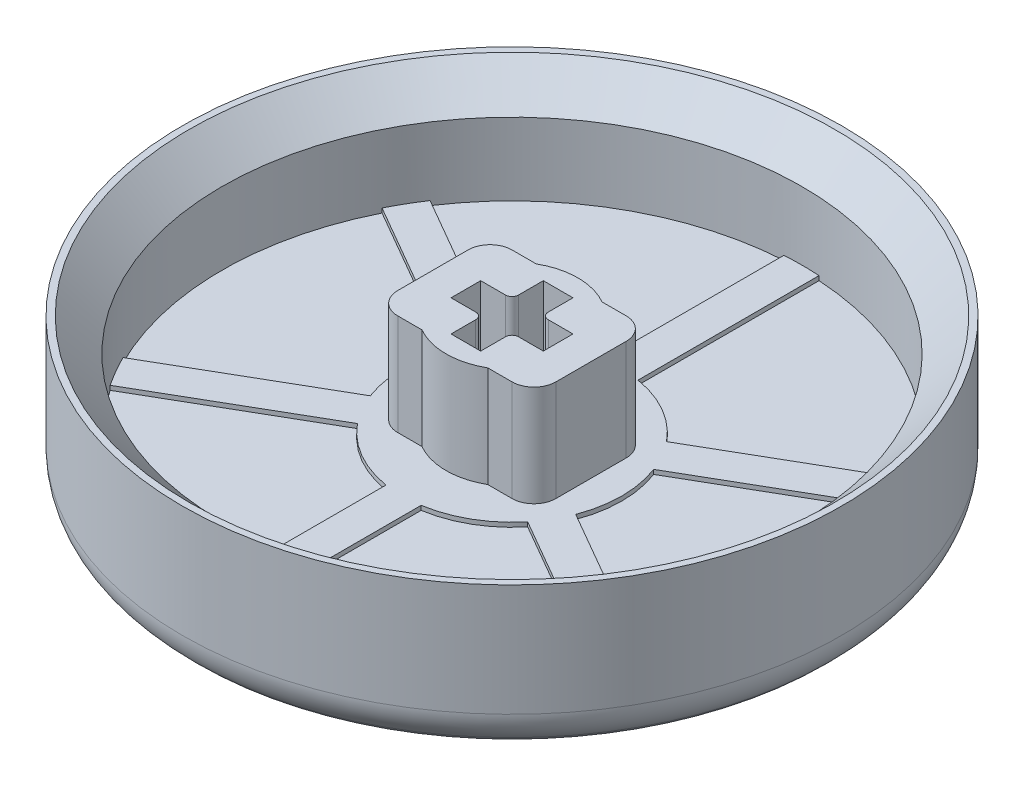
SolidWorks part; units mm, degrees
ref_plane "Front Plane" through (0, 0, 0) normal (0, 0, 1) x (1, 0, 0)
ref_plane "Top Plane" through (0, 0, 0) normal (0, 1, 0) x (1, 0, 0)
ref_plane "Right Plane" through (0, 0, 0) normal (1, 0, 0) x (0, 0, -1)
sketch "Sketch1" plane through (0, 0, 0) normal (0, 1, 0) x (1, 0, 0)
  circle A0 centre (0, 0) radius 15
  dimension "D1" = 30
extrude "button top" add sketch "Sketch1" along normal blind 1.8
sketch "Sketch2" plane through (0, 1.8, 0) normal (0, 1, 0) x (1, 0, 0)
  circle A3 centre (0, 0) radius 15
  circle A4 centre (0, 0) radius 15 construction
  circle A5 centre (0, 0) radius 13.2
  dimension "D1" = 1.8
extrude "button walls" add sketch "Sketch2" along normal blind 4.8
sketch "Sketch5" plane through (0, 1.8, 0) normal (0, 1, 0) x (1, 0, 0)
  circle A0 centre (0, 0) radius 5
  dimension "D1" = 10
extrude "offset" add sketch "Sketch5" along normal blind 0.2
sketch "Sketch3" plane through (0, 1.8, 0) normal (0, 1, 0) x (1, 0, 0)
  line L0 (0, -2.1) -> (0, 2.1) construction
  line L1 (-2.1, 0) -> (2.1, 0) construction
  line L2 (-0.675, 0.975) -> (-0.675, 2.1)
  line L3 (-0.675, -2.1) -> (0.675, -2.1)
  line L4 (-0.675, -2.1) -> (-0.675, -0.975)
  line L5 (-0.675, 2.1) -> (0.675, 2.1)
  line L6 (0.675, -2.1) -> (0.675, -0.975)
  line L7 (-0.675, -2.1) -> (0.675, 2.1) construction
  line L8 (-0.675, 2.1) -> (0.675, -2.1) construction
  line L9 (-2.1, -0.675) -> (-0.975, -0.675)
  line L10 (-2.1, -0.675) -> (-2.1, 0.675)
  line L11 (-2.1, 0.675) -> (-0.975, 0.675)
  line L12 (2.1, -0.675) -> (2.1, 0.675)
  line L13 (-2.1, -0.675) -> (2.1, 0.675) construction
  line L14 (-2.1, 0.675) -> (2.1, -0.675) construction
  line L15 (0.975, 0.675) -> (2.1, 0.675)
  line L16 (0.675, 0.975) -> (0.675, 2.1)
  line L17 (0.975, -0.675) -> (2.1, -0.675)
  line L19 (-3.6, -2.6) -> (3.6, -2.6)
  line L20 (-3.6, -2.6) -> (-3.6, 2.6)
  line L21 (-3.6, 2.6) -> (3.6, 2.6)
  line L22 (3.6, -2.6) -> (3.6, 2.6)
  line L23 (-3.6, -2.6) -> (3.6, 2.6) construction
  line L24 (-3.6, 2.6) -> (3.6, -2.6) construction
  arc A1 (-0.675, -0.975) -> (-0.975, -0.675) centre (-0.975, -0.975) ccw
  arc A2 (0.675, -0.975) -> (0.975, -0.675) centre (0.975, -0.975) cw
  arc A3 (0.975, 0.675) -> (0.675, 0.975) centre (0.975, 0.975) cw
  arc A4 (-0.675, 0.975) -> (-0.975, 0.675) centre (-0.975, 0.975) cw
  circle A5 centre (0, 0) radius 3
  point P0 (0, 0)
  point P6 (0, 0)
  point P9 (0, 0)
  point P22 (2.1, 0)
  point P24 (0, 2.1)
  point P29 (0.675, -0.675)
  point P32 (0.675, 0.675)
  dimension "D1" = 7.2
  dimension "D4" = 0.3
  dimension "D6" = 6
  dimension "D2" = 4.2
  dimension "D3" = 1.35
  dimension "D5" = 5.2
extrude "stem housing" add sketch "Sketch3" along normal blind 4.6 from surface at 0.2 contours A5 L21 L20 L19 | L19 A5 L21 A4 L2 L5 L16 A3 L15 L12 L17 A2 L6 L3 L4 A1 L9 L10 L11 | A5 L19 L22 L21 | L21 A5 | L19 A5 starting at face at (0, 2, 5)
sketch "Sketch4" plane through (0, 1.8, 0) normal (0, 1, 0) x (1, 0, 0)
  line L0 (0, 3.3382) -> (0, 13.2) construction
  line L1 (-0.8, 3.3382) -> (-0.8, 13.2)
  line L2 (0.8, 3.3382) -> (0.8, 13.2)
  line L3 (2.8909, 1.6691) -> (11.4315, 6.6) construction
  line L4 (2.4909, 2.3619) -> (11.0315, 7.2928)
  line L5 (3.2909, 0.9763) -> (11.8315, 5.9072)
  line L6 (2.8909, -1.6691) -> (11.4315, -6.6) construction
  line L7 (3.2909, -0.9763) -> (11.8315, -5.9072)
  line L8 (2.4909, -2.3619) -> (11.0315, -7.2928)
  line L9 (0, -3.3382) -> (0, -13.2) construction
  line L10 (0.8, -3.3382) -> (0.8, -13.2)
  line L11 (-0.8, -3.3382) -> (-0.8, -13.2)
  line L12 (-2.8909, -1.6691) -> (-11.4315, -6.6) construction
  line L13 (-2.4909, -2.3619) -> (-11.0315, -7.2928)
  line L14 (-3.2909, -0.9763) -> (-11.8315, -5.9072)
  line L15 (-2.8909, 1.6691) -> (-11.4315, 6.6) construction
  line L16 (-3.2909, 0.9763) -> (-11.8315, 5.9072)
  line L17 (-2.4909, 2.3619) -> (-11.0315, 7.2928)
  circle A2 centre (0, 0) radius 13.2 construction
  arc A3 (-0.8, 3.3382) -> (0.8, 3.3382) centre (0, 3.3382) ccw
  arc A4 (0.8, 13.2) -> (-0.8, 13.2) centre (0, 13.2) ccw
  arc A5 (2.4909, 2.3619) -> (3.2909, 0.9763) centre (2.8909, 1.6691) ccw
  arc A6 (11.8315, 5.9072) -> (11.0315, 7.2928) centre (11.4315, 6.6) ccw
  arc A7 (3.2909, -0.9763) -> (2.4909, -2.3619) centre (2.8909, -1.6691) ccw
  arc A8 (11.0315, -7.2928) -> (11.8315, -5.9072) centre (11.4315, -6.6) ccw
  arc A9 (0.8, -3.3382) -> (-0.8, -3.3382) centre (0, -3.3382) ccw
  arc A10 (-0.8, -13.2) -> (0.8, -13.2) centre (0, -13.2) ccw
  arc A11 (-2.4909, -2.3619) -> (-3.2909, -0.9763) centre (-2.8909, -1.6691) ccw
  arc A12 (-11.8315, -5.9072) -> (-11.0315, -7.2928) centre (-11.4315, -6.6) ccw
  arc A13 (-3.2909, 0.9763) -> (-2.4909, 2.3619) centre (-2.8909, 1.6691) ccw
  arc A14 (-11.0315, 7.2928) -> (-11.8315, 5.9072) centre (-11.4315, 6.6) ccw
  point P9 (0, 8.2691)
  point P18 (7.1612, 4.1345)
  point P25 (7.1612, -4.1345)
  point P32 (0, -8.2691)
  point P39 (-7.1612, -4.1345)
  point P46 (-7.1612, 4.1345)
  point P51 (0, 0)
  dimension "D1" = 1.6
  dimension "D2" = 6
extrude "spokes" add sketch "Sketch4" along normal up to surface (0.2 mm away) up to face at (0, 2, 5)
fillet "Fillet1" [suppressed] radius 1.5
chamfer "Chamfer1" distance 1.5 angle 45 1 edges at (0, 6.6, 13.2)
fillet "Fillet2" radius 1 4 edges at (-3.6, 4.3, -2.6) (-3.6, 4.3, 2.6) (3.6, 4.3, -2.6) (3.6, 4.3, 2.6)
ref_axis "Axis1" through (0, 0, 0) along (0, 1, 0)
sketch "Sketch6" plane through (0, 0, 0) normal (0, 0, 1) x (1, 0, 0)
  line L0 (-14.2615, 0) -> (-14.4615, 0.2)
  line L1 (-15, 0) -> (15, 0) construction
  line L2 (-15, 6.6) -> (-15, 0) construction
  line L3 (-15, 1.5) -> (-15, 0)
  line L4 (-15, 0) -> (-14.2615, 0)
  arc A0 (-14.4615, 0.2) -> (-15, 1.5) centre (-13.1615, 1.5) cw
  dimension "D1" = 0.2
  dimension "D2" = 1.5
  dimension "D3" = 45
revolve "Cut-Revolve1" cut sketch "Sketch6" angle 360 about axis through (0, 0, 0) along (0, 1, 0)
